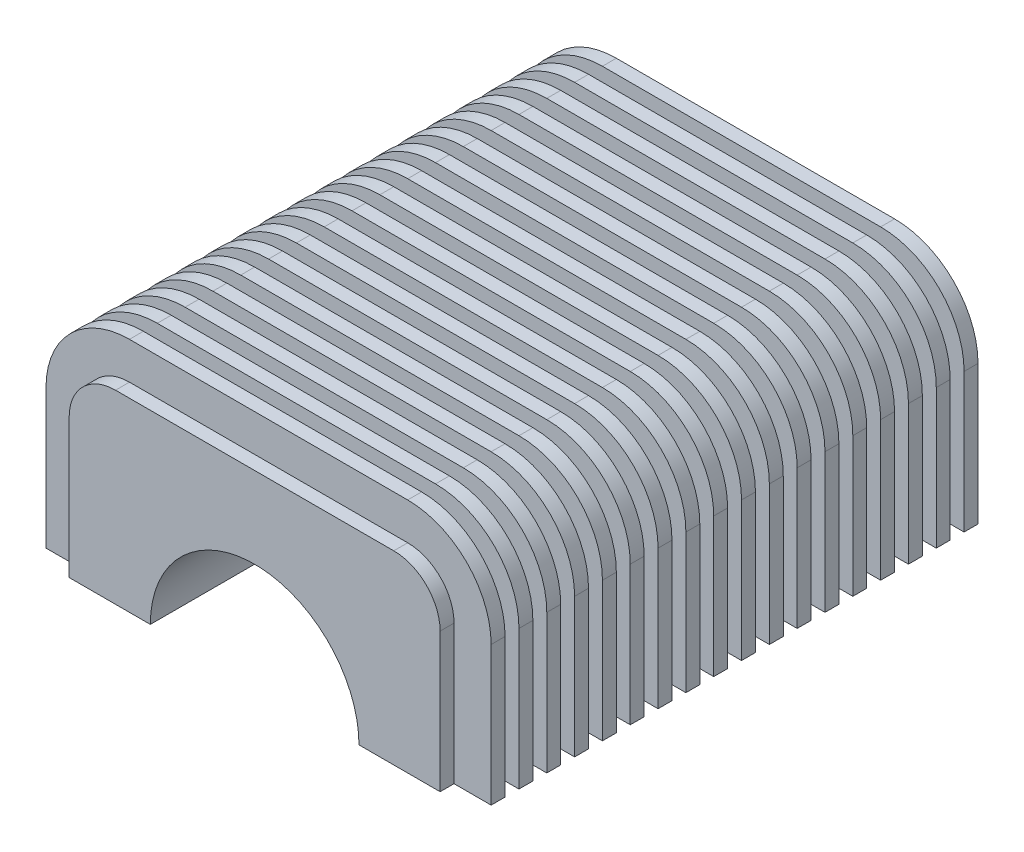
SolidWorks part; units mm, degrees
ref_plane "Płaszczyzna przednia" through (0, 0, 0) normal (0, 0, 1) x (1, 0, 0)
ref_plane "Płaszczyzna górna" through (0, 0, 0) normal (0, 1, 0) x (1, 0, 0)
ref_plane "Płaszczyzna prawa" through (0, 0, 0) normal (1, 0, 0) x (0, 0, -1)
sketch "Szkic1" plane through (0, 0, 0) normal (0, 0, 1) x (1, 0, 0)
  line L0 (22.5, 0) -> (40, 0)
  line L1 (-40, 40) -> (40, 40)
  line L2 (-40, 40) -> (-40, 0)
  line L3 (-40, 0) -> (-22.5, 0)
  line L4 (40, 40) -> (40, 0)
  line L5 (-40, 40) -> (0, 0) construction
  line L6 (0, 0) -> (40, 40) construction
  arc A0 (22.5, 0) -> (-22.5, 0) centre (0, 0) ccw
  dimension "D3" = 45
  dimension "D1" = 80
  dimension "D2" = 40
extrude "Dodanie-wyciągnięcie1" add sketch "Szkic1" along normal blind 108
fillet "Zaokrąglenie1" radius 10 2 edges at (-40, 40, 54) (40, 40, 54)
sketch "Szkic2" plane through (0, 0, 0) normal (0, 0, 1) x (1, 0, 0)
  line L0 (40, 0) -> (48, 0)
  line L5 (30, 40) -> (-30, 40)
  line L6 (-40, 30) -> (-40, 0)
  line L7 (-40, 0) -> (-22.5, 0)
  line L8 (22.5, 0) -> (40, 0)
  line L9 (40, 0) -> (40, 30)
  line L10 (30, 40) -> (-30, 40)
  line L11 (-40, 30) -> (-40, 0)
  line L12 (-40, 0) -> (-22.5, 0)
  line L13 (22.5, 0) -> (40, 0)
  line L14 (40, 0) -> (40, 30)
  line L15 (48, 0) -> (48, 30)
  line L16 (30, 48) -> (-30, 48)
  line L17 (-48, 30) -> (-48, 0)
  line L18 (-40, 0) -> (-48, 0)
  arc A3 (-30, 40) -> (-40, 30) centre (-30, 30) ccw
  arc A4 (22.5, 0) -> (-22.5, 0) centre (0, 0) ccw
  arc A5 (40, 30) -> (30, 40) centre (30, 30) ccw
  arc A6 (-30, 40) -> (-40, 30) centre (-30, 30) ccw
  arc A7 (22.5, 0) -> (-22.5, 0) centre (0, 0) ccw
  arc A8 (40, 30) -> (30, 40) centre (30, 30) ccw
  arc A9 (48, 30) -> (30, 48) centre (30, 30) ccw
  arc A10 (-30, 48) -> (-48, 30) centre (-30, 30) ccw
  dimension "D1" = 0
  dimension "D2" = 8
extrude "Dodanie-wyciągnięcie2" add sketch "Szkic2" along normal blind 3 contours L16 A10 L17 L18 L11 A6 L10 A8 L14 L0 L15 A9
pattern_linear "Szyk liniowy1" count 18 spacing 6 along (0, 0, 1) of "Dodanie-wyciągnięcie2"
